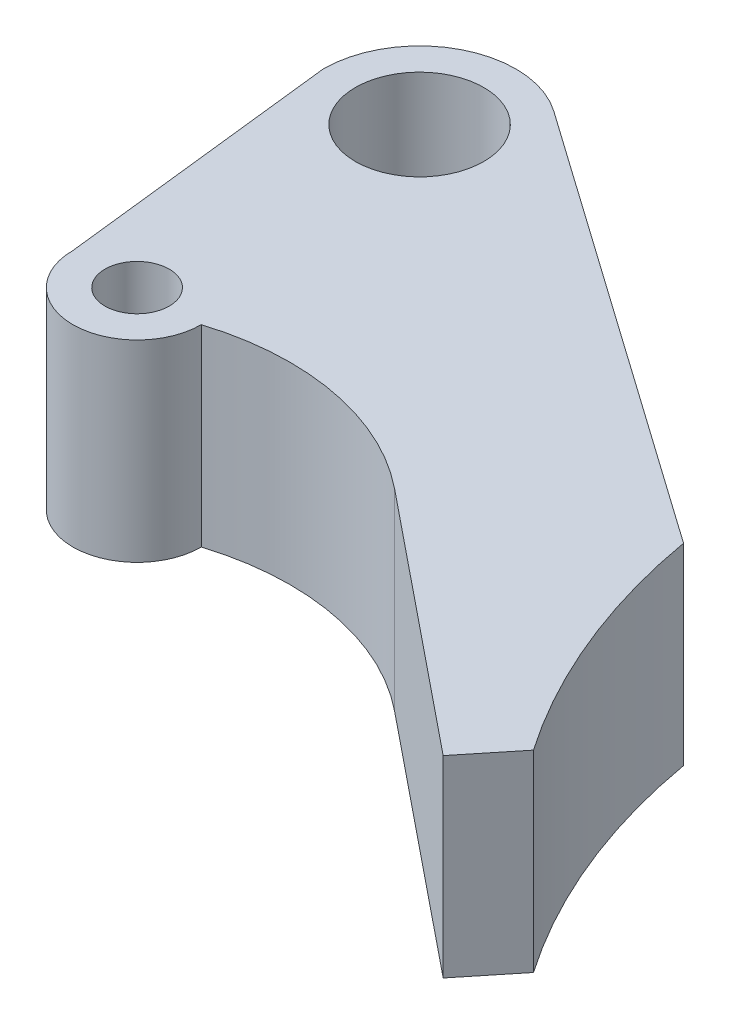
SolidWorks part; units mm, degrees
ref_plane "Front Plane" through (0, 0, 0) normal (0, 0, 1) x (1, 0, 0)
ref_plane "Top Plane" through (0, 0, 0) normal (0, 1, 0) x (1, 0, 0)
ref_plane "Right Plane" through (0, 0, 0) normal (1, 0, 0) x (0, 0, -1)
sketch "Sketch1" plane through (0, 0, 0) normal (0, 1, 0) x (1, 0, 0)
  line L0 (0, 24.0316) -> (0, -19.9684) construction
  line L3 (-41.6359, -19.9684) -> (49.7618, -19.9684) construction
  line L4 (-15, 24.0316) -> (-10, -19.9684)
  line L7 (93.2575, -51.4868) -> (86.9643, -59.2583)
  line L8 (86.9643, -59.2583) -> (47.1767, -27.0389)
  line L10 (77.0362, -11.8909) -> (8.6388, 36.2942)
  line L11 (0, 24.0316) -> (93.2575, -51.4868)
  line L12 (0, 24.0316) -> (77.0362, -11.8909)
  arc A0 (8.6388, 36.2942) -> (-15, 24.0316) centre (0, 24.0316) ccw
  circle A2 centre (0, 24.0316) radius 10
  circle A3 centre (0, -19.9684) radius 5
  arc A4 (-10, -19.9684) -> (10, -19.9684) centre (0, -19.9684) ccw
  arc A6 (47.1767, -27.0389) -> (10, -19.9684) centre (22.0039, -58.1247) ccw
  arc A7 (77.0362, -11.8909) -> (93.2575, -51.4868) centre (175.54, 5.3427) ccw
  point P3 (0, 4.0316)
  dimension "D1" = 20
  dimension "D2" = 15
  dimension "D3" = 10
  dimension "D5" = 65
  dimension "D8" = 90
  dimension "D9" = 80
  dimension "D11" = 10
  dimension "D14" = 200
  dimension "D4" = 44
  dimension "D6" = 51
  dimension "D7" = 10
  dimension "D10" = 120
  dimension "D12" = 90
  dimension "D13" = 85
extrude "Boss-Extrude1" add sketch "Sketch1" along normal blind 30 contours A7 L12 A2 L11 | A6 L8 L7 L11 A2 L12 L10 A0 L4 A4 A3
